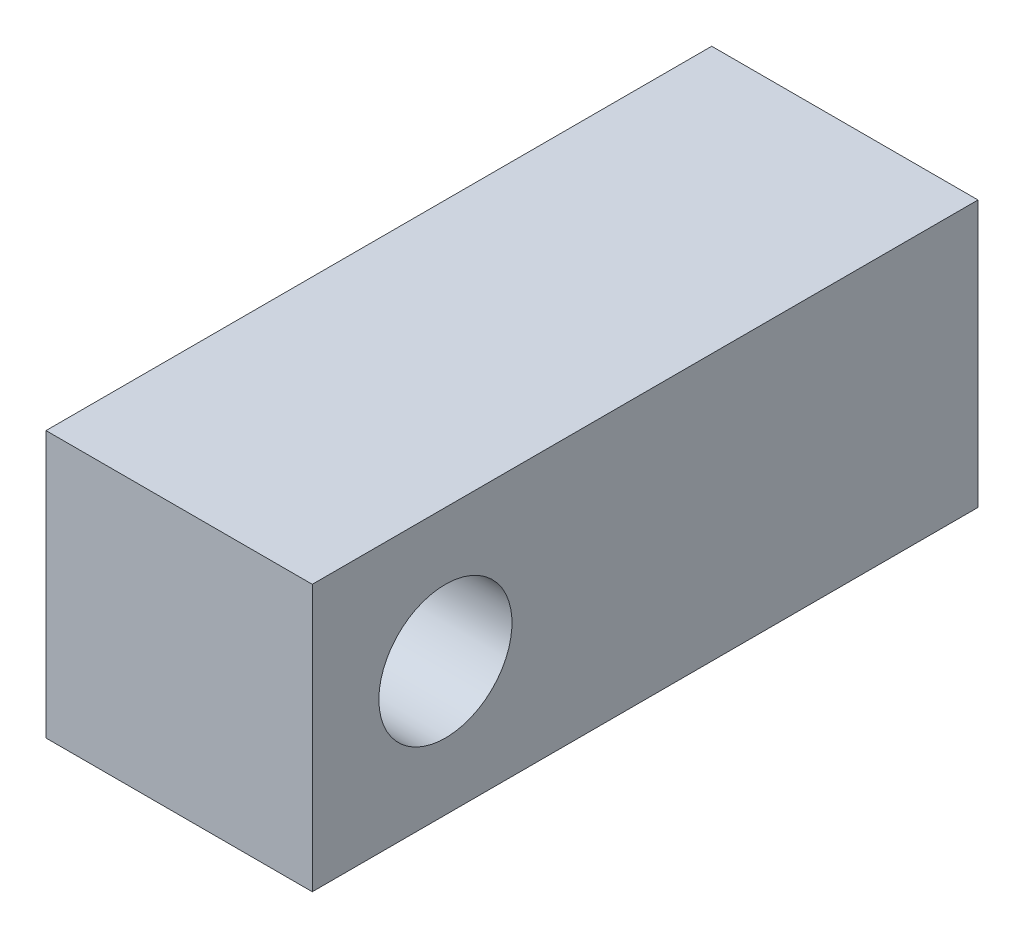
SolidWorks part; units mm, degrees
ref_plane "Front Plane" through (0, 0, 0) normal (0, 0, 1) x (1, 0, 0)
ref_plane "Top Plane" through (0, 0, 0) normal (0, 1, 0) x (1, 0, 0)
ref_plane "Right Plane" through (0, 0, 0) normal (1, 0, 0) x (0, 0, -1)
sketch "Sketch1" plane through (0, 0, 0) normal (0, 0, 1) x (1, 0, 0)
  line L1 (-4.3645, 7.6422) -> (-29.7645, 7.6422)
  line L2 (-4.3645, 7.6422) -> (-4.3645, 33.0422)
  line L3 (-4.3645, 33.0422) -> (-29.7645, 33.0422)
  line L4 (-29.7645, 7.6422) -> (-29.7645, 33.0422)
  dimension "D1" = 25.4
  dimension "D2" = 25.4
extrude "Boss-Extrude1" add sketch "Sketch1" along normal blind 63.5
sketch "Sketch2" plane through (-29.7645, 0, 0) normal (-1, 0, 0) x (0, 0, 1)
  line L0 (63.5, 33.0422) -> (63.5, 7.6422) construction
  line L1 (63.5, 7.6422) -> (0, 7.6422) construction
  circle A0 centre (50.8, 20.3422) radius 6.35
  dimension "D1" = 12.7
  dimension "D2" = 12.7
extrude "Cut-Extrude1" cut sketch "Sketch2" against normal through all
